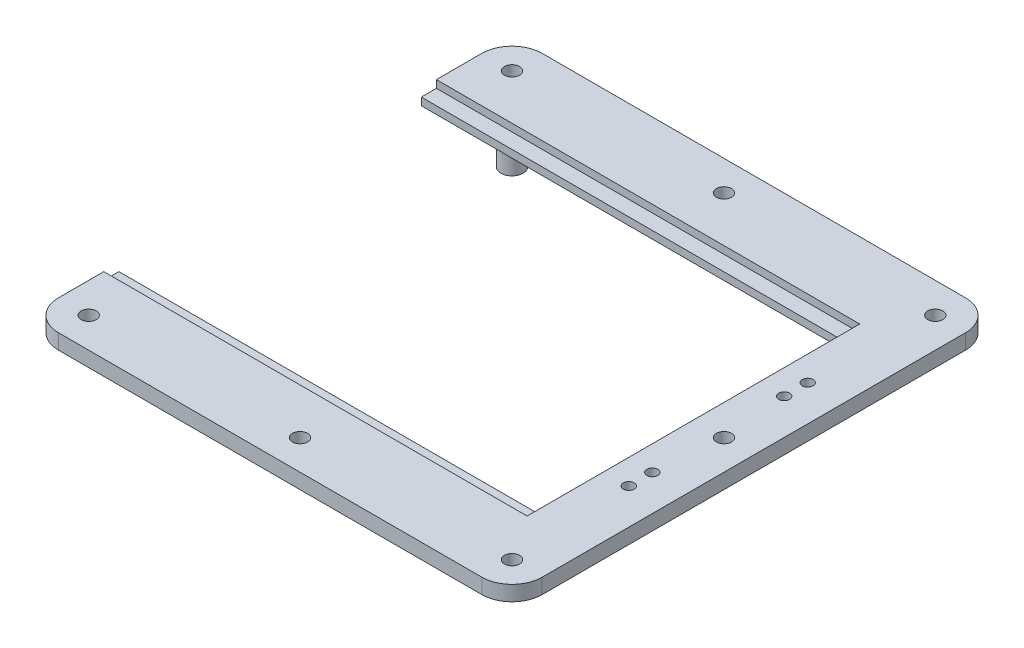
SolidWorks part; units mm, degrees
ref_plane "Front Plane" through (0, 0, 0) normal (0, 0, 1) x (1, 0, 0)
ref_plane "Top Plane" through (0, 0, 0) normal (0, 1, 0) x (1, 0, 0)
ref_plane "Right Plane" through (0, 0, 0) normal (1, 0, 0) x (0, 0, -1)
sketch "Sketch1" plane through (0, 0, 0) normal (0, 1, 0) x (1, 0, 0)
  line L0 (0, 0) -> (0, 25.4)
  line L1 (12.7, 38.1) -> (190.5, 38.1)
  line L2 (203.2, 25.4) -> (203.2, -152.4)
  line L3 (190.5, -165.1) -> (12.7, -165.1)
  line L4 (0, -152.4) -> (0, -127)
  line L5 (0, -127) -> (177.8, -127)
  line L6 (177.8, -127) -> (177.8, 0)
  line L7 (177.8, 0) -> (0, 0)
  arc A0 (12.7, -165.1) -> (0, -152.4) centre (12.7, -152.4) cw
  arc A1 (203.2, -152.4) -> (190.5, -165.1) centre (190.5, -152.4) cw
  arc A2 (190.5, 38.1) -> (203.2, 25.4) centre (190.5, 25.4) cw
  arc A3 (0, 25.4) -> (12.7, 38.1) centre (12.7, 25.4) cw
  point P13 (203.2, -165.1)
  point P16 (203.2, 38.1)
  point P19 (0, 38.1)
  dimension "D6" = 12.7
  dimension "D1" = 203.2
  dimension "D2" = 38.1
  dimension "D3" = 203.2
  dimension "D4" = 177.8
  dimension "D5" = 127
extrude "Boss-Extrude2" add sketch "Sketch1" along normal blind 6.35
sketch "Sketch2" plane through (0, 6.35, 0) normal (0, 1, 0) x (1, 0, 0)
  circle A0 centre (12.7, 25.4) radius 3.175
  circle A1 centre (190.5, 25.4) radius 3.175
  circle A2 centre (190.5, -152.4) radius 3.175
  circle A3 centre (12.7, -152.4) radius 3.175
  arc A4 (12.7, 38.1) -> (0, 25.4) centre (12.7, 25.4) ccw construction
  dimension "D1" = 6.35
extrude "Cut-Extrude1" cut sketch "Sketch2" against normal through all
sketch "Sketch5" plane through (0, 0, 0) normal (0, -1, 0) x (1, 0, 0)
  line L0 (0, 127) -> (0, 152.4) construction
  line L1 (12.7, 165.1) -> (190.5, 165.1) construction
  line L2 (203.2, 152.4) -> (203.2, -25.4) construction
  line L4 (203.2, 63.5) -> (0, 63.5) construction
  circle A0 centre (28.575, 136.525) radius 4.6625
  circle A1 centre (174.625, 136.525) radius 4.6625
  circle A4 centre (174.625, -9.525) radius 4.6625
  circle A5 centre (28.575, -9.525) radius 4.6625
  dimension "D1" = 28.575
  dimension "D2" = 28.575
  dimension "D3" = 9.325
  dimension "D4" = 28.575
  dimension "D5" = 28.575
extrude "Boss-Extrude3" add sketch "Sketch5" along normal blind 12.7
sketch "Sketch6" plane through (0, 6.35, 0) normal (0, 1, 0) x (1, 0, 0)
  line L0 (0, -127) -> (0, -152.4) construction
  line L1 (177.8, -127) -> (0, -127)
  line L2 (177.8, -127) -> (177.8, -133.35)
  line L3 (177.8, -133.35) -> (0, -133.35)
  line L4 (0, -127) -> (0, -133.35)
  line L5 (203.2, -63.5) -> (0, -63.5) construction
  line L6 (203.2, -152.4) -> (203.2, 25.4) construction
  line L7 (0, 0) -> (0, 6.35)
  line L8 (177.8, 6.35) -> (0, 6.35)
  line L9 (177.8, 0) -> (177.8, 6.35)
  line L10 (177.8, 0) -> (0, 0)
  dimension "D1" = 6.35
extrude "Cut-Extrude2" cut sketch "Sketch6" against normal blind 3.175
sketch "Sketch7" plane through (0, 6.35, 0) normal (0, 1, 0) x (1, 0, 0)
  line L0 (188.214, -28.194) -> (188.214, -33.528) construction
  line L1 (188.214, -38.1) -> (188.214, -88.9) construction
  line L2 (188.214, -93.472) -> (188.214, -98.806) construction
  line L3 (188.214, -23.622) -> (188.214, 38.1) construction
  line L4 (190.5, 38.1) -> (12.7, 38.1) construction
  line L5 (188.214, -103.378) -> (188.214, -165.1) construction
  line L6 (12.7, -165.1) -> (190.5, -165.1) construction
  line L7 (185.928, -25.908) -> (177.8, -25.908) construction
  line L8 (177.8, 6.35) -> (177.8, -133.35) construction
  circle A0 centre (188.214, -101.092) radius 2.286
  circle A1 centre (188.214, -91.186) radius 2.286
  circle A2 centre (188.214, -35.814) radius 2.286
  circle A3 centre (188.214, -25.908) radius 2.286
  dimension "D1" = 4.572
  dimension "D2" = 5.334
  dimension "D3" = 5.334
  dimension "D4" = 50.8
  dimension "D5" = 8.128
extrude "Cut-Extrude3" cut sketch "Sketch7" against normal blind 12.7
sketch "Sketch8" plane through (0, 6.35, 0) normal (0, 1, 0) x (1, 0, 0)
  line L0 (12.7, -152.4) -> (190.5, 25.4) construction
  line L1 (12.7, 25.4) -> (190.5, -152.4) construction
  line L2 (190.5, 38.1) -> (12.7, 38.1) construction
  circle A0 centre (101.6, 25.527) radius 3.175
  circle A1 centre (190.627, -63.5) radius 3.175
  circle A2 centre (101.6, -152.527) radius 3.175
  circle A4 centre (12.573, -63.5) radius 3.175 [skipped]
  point P12 (101.6, 38.1)
  point P13 (101.6, -63.5)
  dimension "D3" = 6.35
  dimension "D2" = 12.573
  dimension "D1" = 4
extrude "Cut-Extrude4" cut sketch "Sketch8" against normal through all
